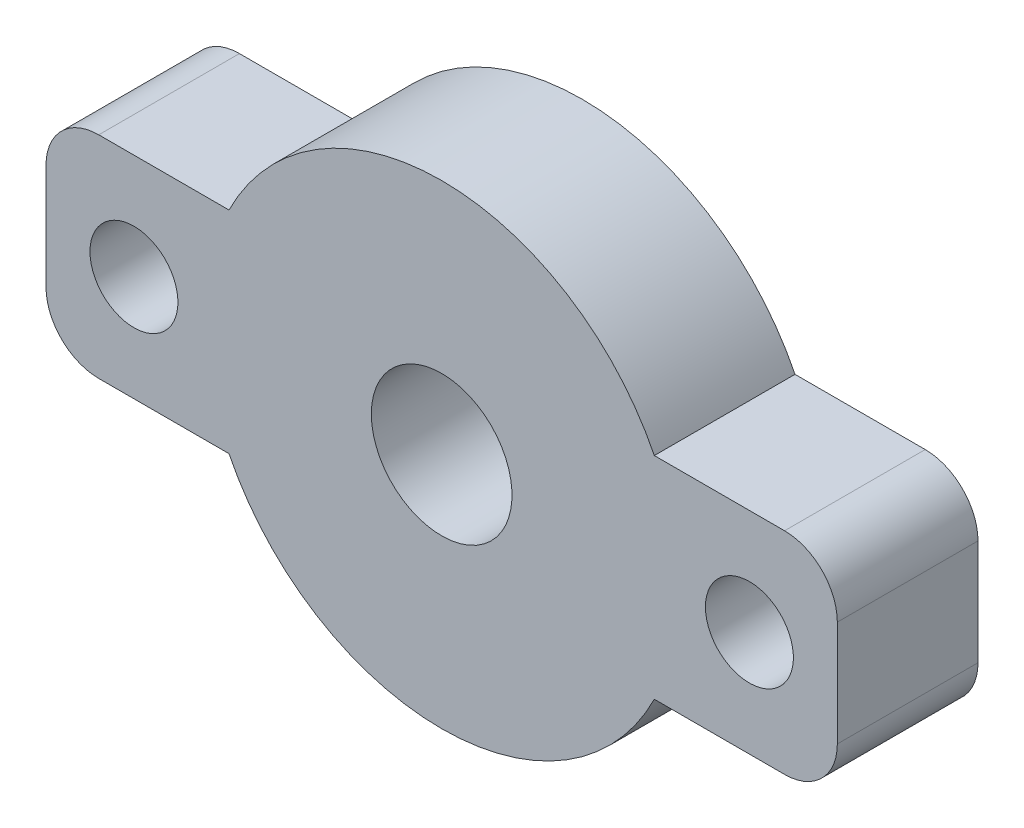
SolidWorks part; units mm, degrees
ref_plane "前视基准面" through (0, 0, 0) normal (0, 0, 1) x (1, 0, 0)
ref_plane "上视基准面" through (0, 0, 0) normal (0, 1, 0) x (1, 0, 0)
ref_plane "右视基准面" through (0, 0, 0) normal (1, 0, 0) x (0, 0, -1)
sketch "草图1" plane through (0, 0, 0) normal (0, 0, 1) x (1, 0, 0)
  circle A0 centre (0, 0) radius 13.5
extrude "凸台-拉伸1" add sketch "草图1" along normal blind 8
sketch "草图3" plane through (0, 0, 8) normal (0, 0, 1) x (1, 0, 0)
  line L1 (22.5, -6) -> (-22.5, -6)
  line L2 (22.5, -6) -> (22.5, 6)
  line L3 (22.5, 6) -> (-22.5, 6)
  line L4 (-22.5, -6) -> (-22.5, 6)
  line L5 (22.5, -6) -> (-22.5, 6) construction
  line L6 (22.5, 6) -> (-22.5, -6) construction
  point P0 (0, 0)
extrude "凸台-拉伸2" add sketch "草图3" against normal up to surface (8 mm away) up to face at (13.5, 0, 0)
sketch "草图2" plane through (0, 0, 0) normal (0, 0, -1) x (-1, 0, 0)
  circle A0 centre (0, 0) radius 4
extrude "切除-拉伸1" cut sketch "草图2" against normal blind 8
sketch "草图4" plane through (0, 0, 0) normal (0, 0, -1) x (-1, 0, 0)
  line L0 (-17.5, 0) -> (17.5, 0) construction
  circle A0 centre (-17.5, 0) radius 2.5
  circle A1 centre (17.5, 0) radius 2.5
  point P3 (0, 0)
extrude "切除-拉伸2" cut sketch "草图4" against normal through all
fillet "圆角1" radius 3 4 edges at (-22.5, -6, 4) (-22.5, 6, 4) (22.5, -6, 4) (22.5, 6, 4)
